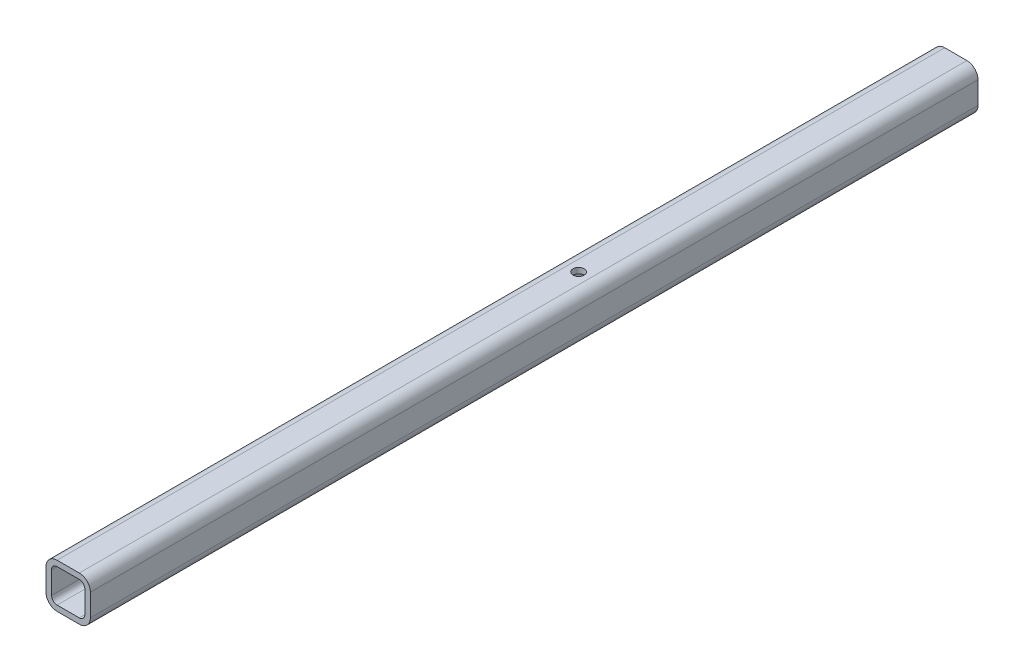
SolidWorks part; units mm, degrees
ref_plane "Front Plane" through (0, 0, 0) normal (0, 0, 1) x (1, 0, 0)
ref_plane "Top Plane" through (0, 0, 0) normal (0, 1, 0) x (1, 0, 0)
ref_plane "Right Plane" through (0, 0, 0) normal (1, 0, 0) x (0, 0, -1)
sketch "Sketch1" plane through (0, 0, 0) normal (0, 0, 1) x (1, 0, 0)
  line L0 (12.7, 6.35) -> (38.1, 6.35)
  line L1 (6.35, 12.7) -> (6.35, 38.1)
  line L2 (38.1, 44.45) -> (12.7, 44.45)
  line L3 (44.45, 38.1) -> (44.45, 12.7)
  line L4 (12.7, 0) -> (38.1, 0)
  line L5 (0, 12.7) -> (0, 38.1)
  line L6 (38.1, 50.8) -> (12.7, 50.8)
  line L7 (50.8, 38.1) -> (50.8, 12.7)
  arc A0 (50.8, 38.1) -> (38.1, 50.8) centre (38.1, 38.1) ccw
  arc A1 (38.1, 0) -> (50.8, 12.7) centre (38.1, 12.7) ccw
  arc A2 (0, 12.7) -> (12.7, 0) centre (12.7, 12.7) ccw
  arc A3 (12.7, 50.8) -> (0, 38.1) centre (12.7, 38.1) ccw
  arc A4 (12.7, 44.45) -> (6.35, 38.1) centre (12.7, 38.1) ccw
  arc A5 (44.45, 38.1) -> (38.1, 44.45) centre (38.1, 38.1) ccw
  arc A6 (38.1, 6.35) -> (44.45, 12.7) centre (38.1, 12.7) ccw
  arc A7 (6.35, 12.7) -> (12.7, 6.35) centre (12.7, 12.7) ccw
  dimension "D1" = 12.7
  dimension "Thickness" = 6.35
  dimension "V_leg" = 50.8
  dimension "H_leg" = 50.8
extrude "Boss-Extrude1" add sketch "Sketch1" along normal mid plane 1016
hole_wizard "1/2 (0.5) Diameter Hole1" positions "Sketch3" profile "Sketch4" hole size "1/2" standard "Ansi Inch" end condition through all
sketch "Sketch3" plane through (0, 50.8, 0) normal (0, 1, 0) x (-1, 0, 0)
  line L1 (0, 508) -> (0, -508) construction
  line L3 (-38.1, 508) -> (-12.7, 508) construction
  point P0 (-25.4, -76.2)
  dimension "D1" = 584.2
  dimension "D2" = 25.4
sketch "Sketch4" plane through (25.4, 50.8, -76.2) normal (1, 0, 0) x (0, 0, 1)
  line L0 (0, 0) -> (0, 50.8)
  line L1 (0, 50.8) -> (6.35, 50.8)
  line L2 (6.35, 50.8) -> (6.35, 0)
  line L5 (6.35, 0) -> (0, 0)
  line L11 (0, -6.35) -> (0, 107.95) construction
  dimension "Thru Hole Dia." = 12.7
  dimension "Thru Hole Depth" = 50.8
sketch "Sketch8" plane through (50.8, 0, 0) normal (1, 0, 0) x (0, 0, -1)
  line L1 (508, 12.7) -> (508, 38.1) construction
  line L2 (457.2, 50.8) -> (508, 50.8)
  line L3 (508, 50.8) -> (508, 12.7)
  line L4 (-508, 50.8) -> (508, 50.8) construction
  line L5 (508, 12.7) -> (457.2, 12.7)
  line L6 (-508, 12.7) -> (508, 12.7) construction
  line L7 (457.2, 12.7) -> (457.2, 50.8)
  dimension "D1" = 38.1
  dimension "D2" = 50.8
sketch "Sketch9" plane through (0, 0, 0) normal (0, -1, 0) x (1, 0, 0)
  line L0 (25.4, -488.95) -> (25.4, -469.9) construction
  line L1 (19.05, -488.95) -> (19.05, -469.9)
  line L2 (31.75, -488.95) -> (31.75, -469.9)
  line L3 (12.7, -508) -> (38.1, -508) construction
  line L4 (25.4, -508) -> (25.4, -488.95) construction
  arc A0 (19.05, -488.95) -> (31.75, -488.95) centre (25.4, -488.95) ccw
  arc A1 (31.75, -469.9) -> (19.05, -469.9) centre (25.4, -469.9) ccw
  point P2 (25.4, -479.425)
  dimension "D2" = 6.35
  dimension "D1" = 19.05
  dimension "D3" = 19.05
extrude "Cut-Extrude3" cut sketch "Sketch9" against normal up to next
